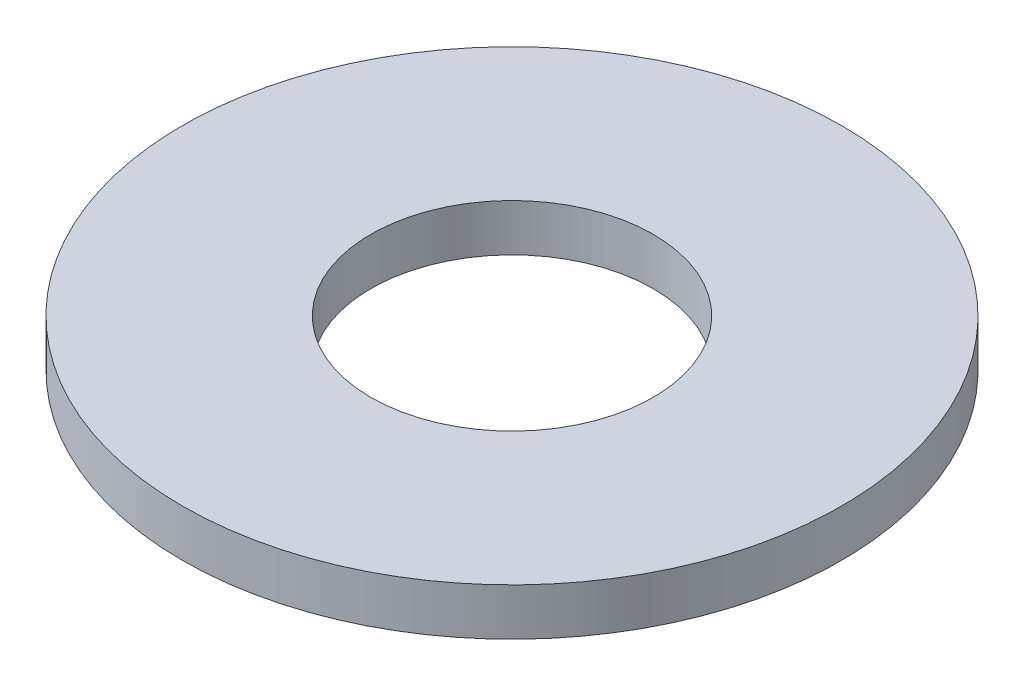
SolidWorks part; units mm, degrees
ref_plane "前视基准面" through (0, 0, 0) normal (0, 0, 1) x (1, 0, 0)
ref_plane "上视基准面" through (0, 0, 0) normal (0, 1, 0) x (1, 0, 0)
ref_plane "右视基准面" through (0, 0, 0) normal (1, 0, 0) x (0, 0, -1)
sketch "草图1" plane through (0, 0, 0) normal (0, 1, 0) x (1, 0, 0)
  circle A0 centre (0, 0) radius 3.5
  circle A1 centre (0, 0) radius 1.5
  dimension "D1" = 3
  dimension "D2" = 7
extrude "凸台-拉伸1" add sketch "草图1" along normal blind 0.5
